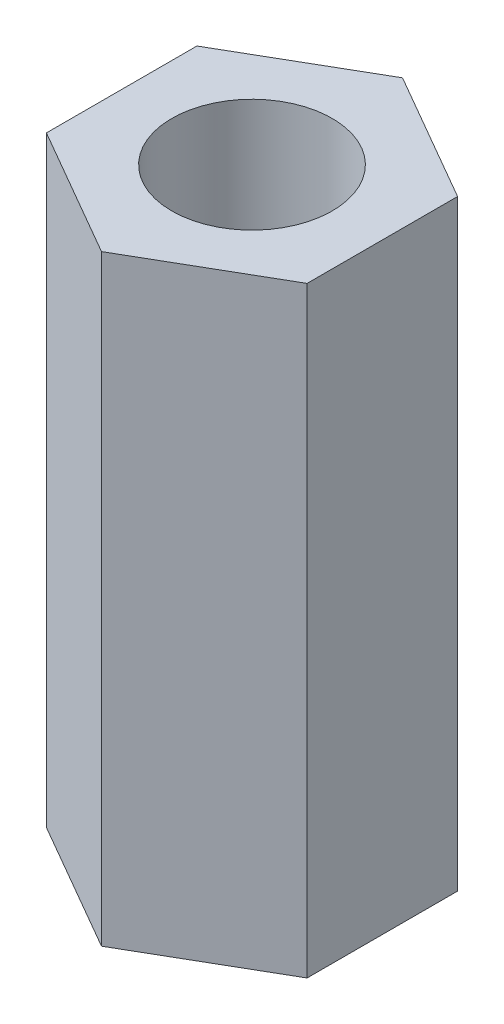
SolidWorks part; units mm, degrees
ref_plane "Спереди" through (0, 0, 0) normal (0, 0, 1) x (1, 0, 0)
ref_plane "Сверху" through (0, 0, 0) normal (0, 1, 0) x (1, 0, 0)
ref_plane "Справа" through (0, 0, 0) normal (1, 0, 0) x (0, 0, -1)
sketch "Эскиз1" plane through (0, 0, 0) normal (0, 1, 0) x (1, 0, 0)
  line L1 (0, 7.5056) -> (-6.5, 3.7528)
  line L2 (-6.5, 3.7528) -> (-6.5, -3.7528)
  line L3 (-6.5, -3.7528) -> (0, -7.5056)
  line L4 (0, -7.5056) -> (6.5, -3.7528)
  line L5 (6.5, -3.7528) -> (6.5, 3.7528)
  line L6 (6.5, 3.7528) -> (0, 7.5056)
  circle A0 centre (0, 0) radius 6.5 construction
  circle A1 centre (0, 0) radius 4
extrude "Бобышка-Вытянуть1" add sketch "Эскиз1" along normal blind 30
